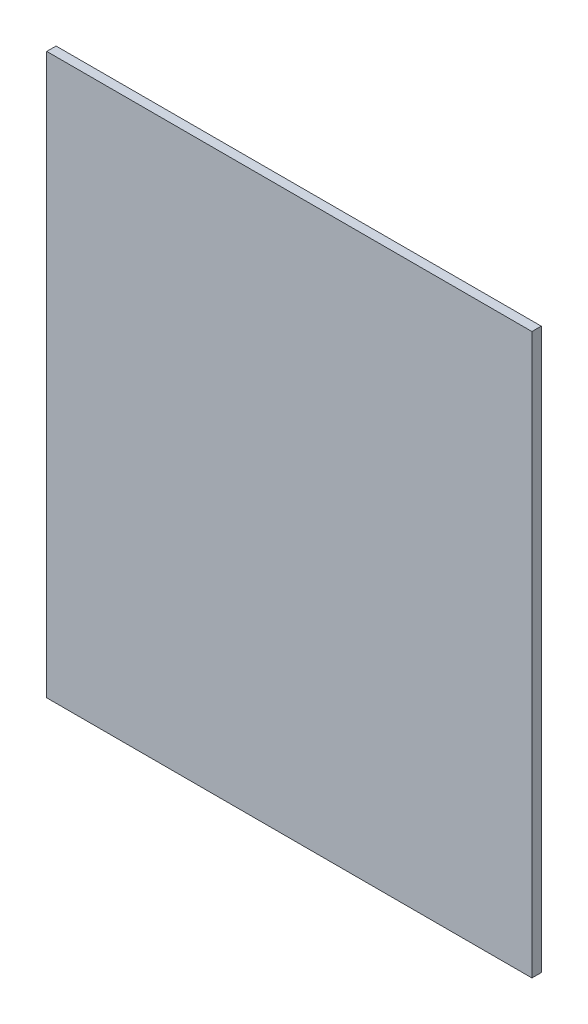
SolidWorks part; units mm, degrees
material "ALUMINUM 6061-T6"
ref_plane "Front Plane" through (0, 0, 0) normal (0, 0, 1) x (1, 0, 0)
ref_plane "Top Plane" through (0, 0, 0) normal (0, 1, 0) x (1, 0, 0)
ref_plane "Right Plane" through (0, 0, 0) normal (1, 0, 0) x (0, 0, -1)
sketch "Sketch1" plane through (0, 0, 0) normal (0, 0, 1) x (1, 0, 0)
  line L1 (-165.1, -190.5) -> (165.1, -190.5)
  line L2 (-165.1, -190.5) -> (-165.1, 190.5)
  line L3 (-165.1, 190.5) -> (165.1, 190.5)
  line L4 (165.1, -190.5) -> (165.1, 190.5)
  line L5 (-165.1, -190.5) -> (165.1, 190.5) construction
  line L6 (-165.1, 190.5) -> (165.1, -190.5) construction
  point P0 (0, 0)
  dimension "D1" = 330.2
  dimension "D2" = 381
extrude "Boss-Extrude1" add sketch "Sketch1" along normal mid plane 6.35
